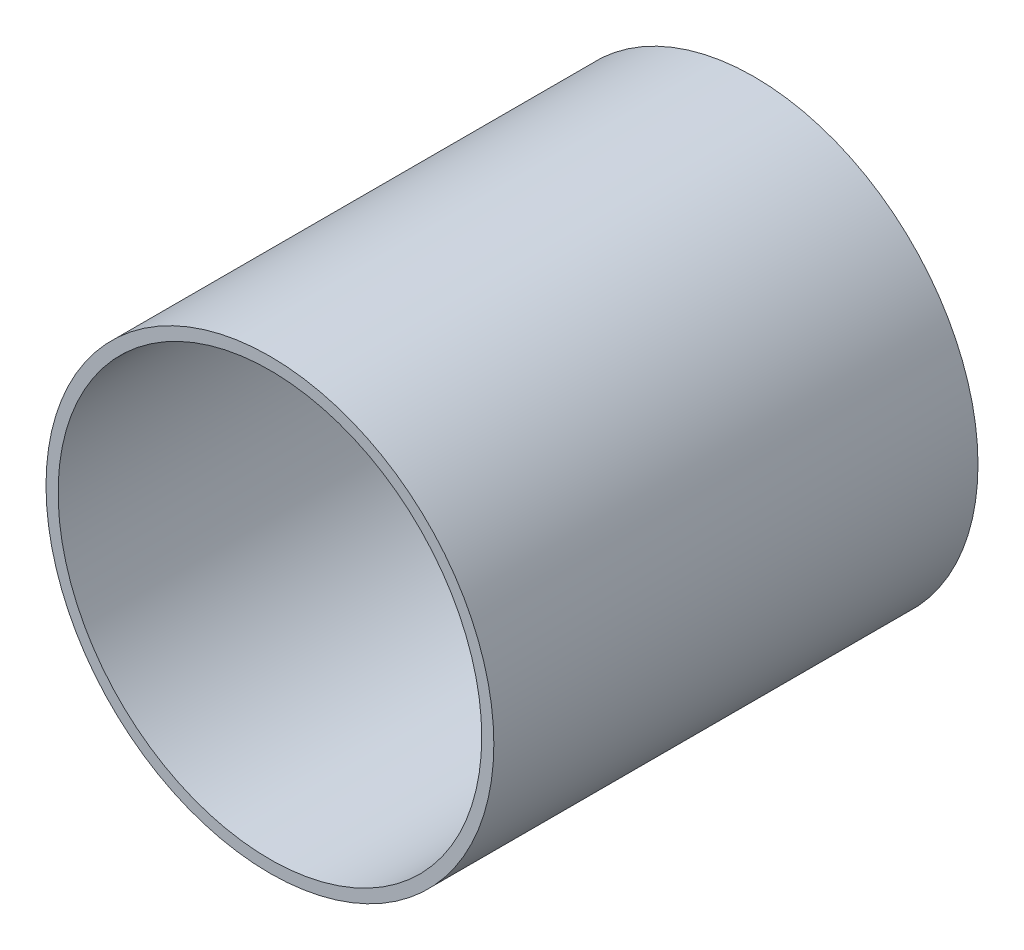
SolidWorks part; units mm, degrees
ref_plane "Front Plane" through (0, 0, 0) normal (0, 0, 1) x (1, 0, 0)
ref_plane "Top Plane" through (0, 0, 0) normal (0, 1, 0) x (1, 0, 0)
ref_plane "Right Plane" through (0, 0, 0) normal (1, 0, 0) x (0, 0, -1)
sketch "Sketch1" plane through (0, 0, 0) normal (0, 0, 1) x (1, 0, 0)
  circle A0 centre (0, 0) radius 7
  dimension "D1" = 14
extrude "Extrude-Thin1" add sketch "Sketch1" along normal blind 16 thin
